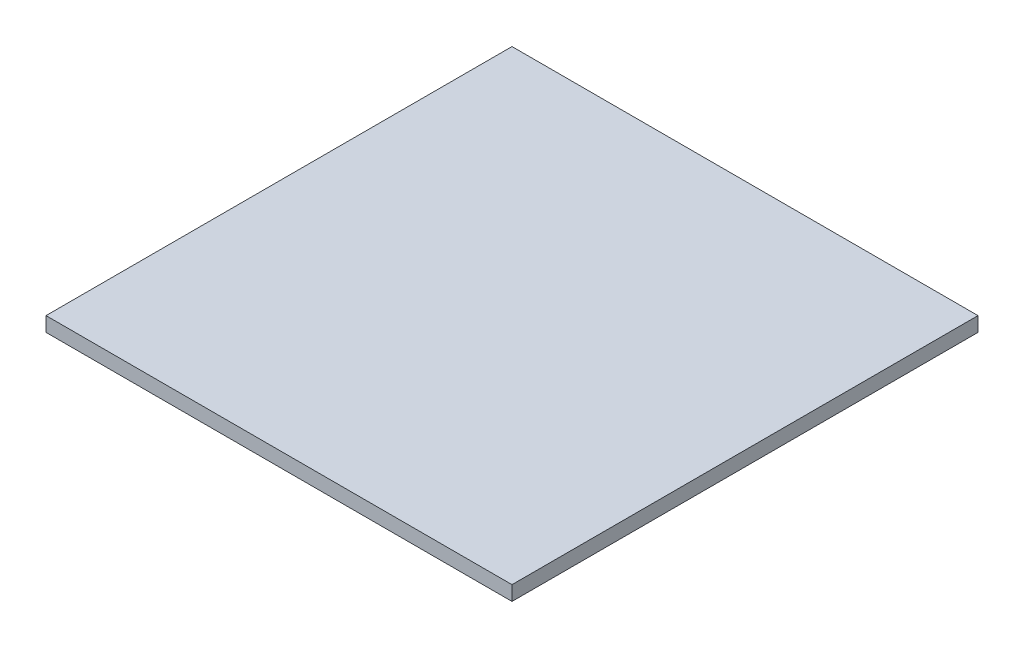
SolidWorks part; units mm, degrees
ref_plane "Front Plane" through (0, 0, 0) normal (0, 0, 1) x (1, 0, 0)
ref_plane "Top Plane" through (0, 0, 0) normal (0, 1, 0) x (1, 0, 0)
ref_plane "Right Plane" through (0, 0, 0) normal (1, 0, 0) x (0, 0, -1)
sketch "Sketch1" plane through (0, 0, 0) normal (0, 1, 0) x (1, 0, 0)
  line L1 (0, 0) -> (203.2, 0)
  line L2 (0, 0) -> (0, 203.2)
  line L3 (0, 203.2) -> (203.2, 203.2)
  line L4 (203.2, 0) -> (203.2, 203.2)
  dimension "D1" = 203.2
  dimension "D2" = 203.2
extrude "Boss-Extrude1" add sketch "Sketch1" along normal blind 6.35
